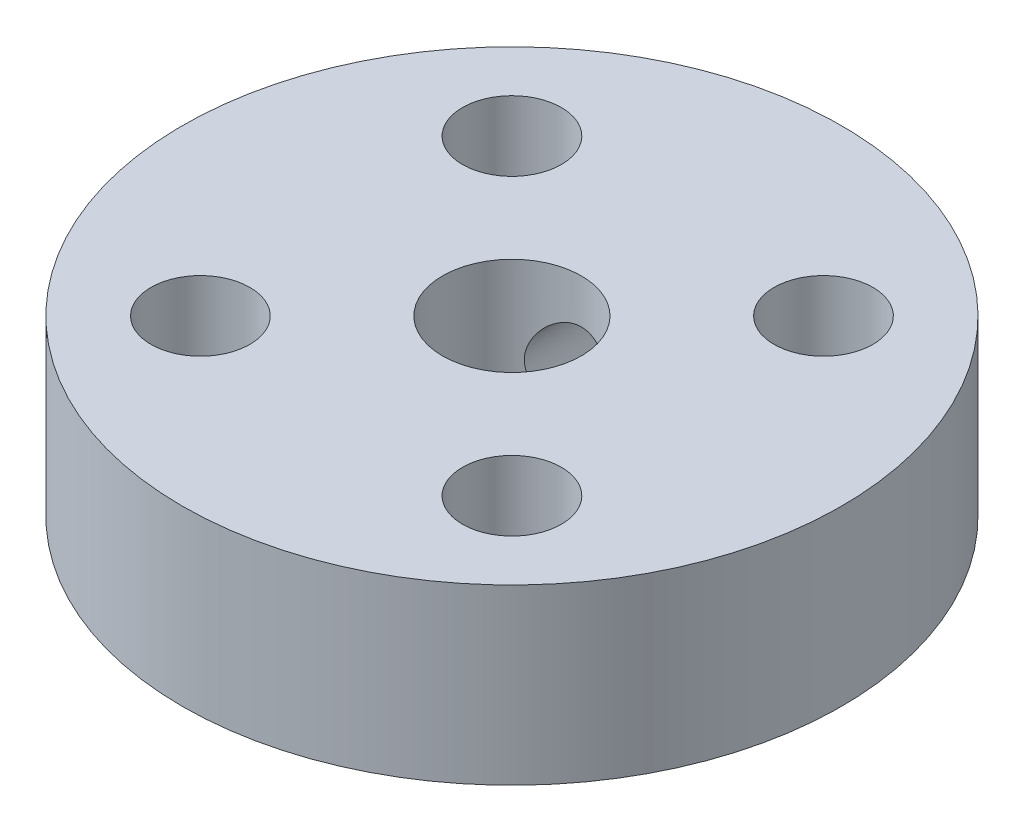
SolidWorks part; units mm, degrees
ref_plane "Front Plane" through (0, 0, 0) normal (0, 0, 1) x (1, 0, 0)
ref_plane "Top Plane" through (0, 0, 0) normal (0, 1, 0) x (1, 0, 0)
ref_plane "Right Plane" through (0, 0, 0) normal (1, 0, 0) x (0, 0, -1)
sketch "Sketch1" plane through (0, 0, 0) normal (0, 1, 0) x (1, 0, 0)
  line L0 (0, 9.5) -> (0, -9.5) construction
  line L1 (-9.5, 0) -> (9.5, 0) construction
  line L2 (0, 0) -> (-6.7175, 6.7175) construction
  circle A0 centre (0, 0) radius 9.5
  circle A1 centre (0, 0) radius 2
  circle A2 centre (-4.4901, 4.4901) radius 1.425
  circle A3 centre (4.4901, 4.4901) radius 1.425
  circle A4 centre (4.4901, -4.4901) radius 1.425
  circle A5 centre (-4.4901, -4.4901) radius 1.425
  dimension "D1" = 19
  dimension "D2" = 4
  dimension "D5" = 2.85
  dimension "D3" = 45
  dimension "D4" = 6.35
extrude "Boss-Extrude1" add sketch "Sketch1" along normal blind 5
ref_plane "Plane1" through (0, 0, -9.5) normal (0, 0, -1) x (-1, 0, 0)
sketch "Sketch2" plane through (0, 0, -9.5) normal (0, 0, -1) x (-1, 0, 0)
  line L0 (-9.5, 2.5) -> (9.5, 2.5) construction
  line L1 (-9.5, 5) -> (-9.5, 0) construction
  line L2 (9.5, 0) -> (9.5, 5) construction
  circle A0 centre (0, 2.5) radius 1.225
  dimension "D1" = 2.45
extrude "Cut-Extrude1" cut sketch "Sketch2" against normal up to next
